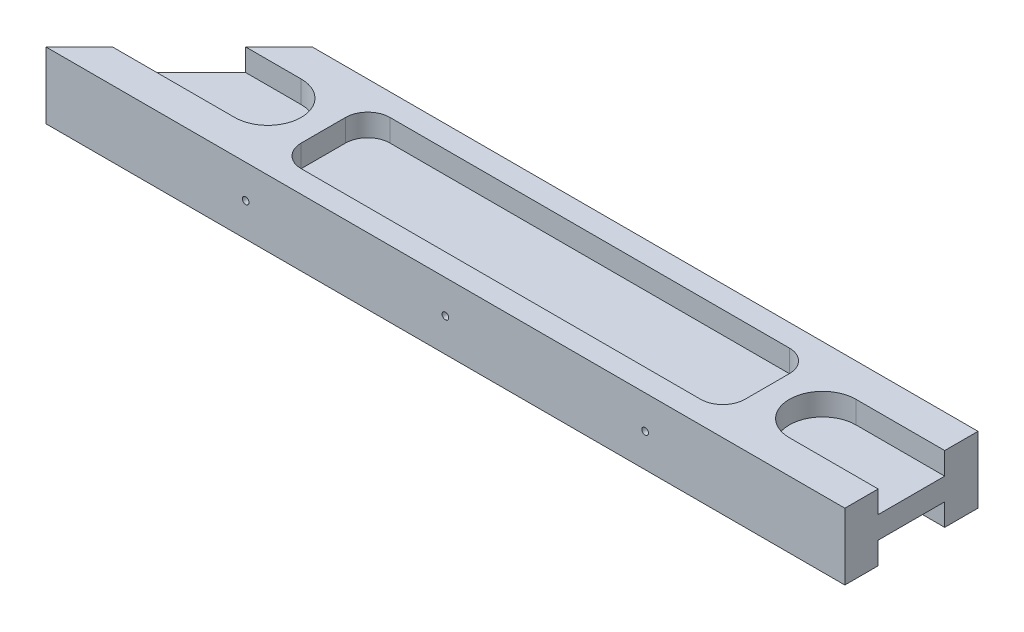
SolidWorks part; units mm, degrees
ref_plane "Front Plane" through (0, 0, 0) normal (0, 0, 1) x (1, 0, 0)
ref_plane "Top Plane" through (0, 0, 0) normal (0, 1, 0) x (1, 0, 0)
ref_plane "Right Plane" through (0, 0, 0) normal (1, 0, 0) x (0, 0, -1)
sketch "Sketch1" plane through (0, 0, 0) normal (0, 1, 0) x (1, 0, 0)
  line L0 (0, 0) -> (180, 0)
  line L1 (180, 0) -> (180, 30)
  line L2 (180, 30) -> (30, 30)
  line L3 (30, 30) -> (0, 0)
  dimension "D1" = 150
  dimension "D2" = 180
  dimension "D3" = 30
extrude "Boss-Extrude1" add sketch "Sketch1" along normal blind 15
sketch "Sketch2" plane through (0, 15, 0) normal (0, 1, 0) x (1, 0, 0)
  line L0 (-5, 15) -> (35, 15) construction
  line L1 (-5, 22.5) -> (35, 22.5)
  line L2 (-5, 7.5) -> (35, 7.5)
  line L3 (30, 30) -> (0, 0) construction
  line L4 (15, 15) -> (180, 15) construction
  line L7 (180, 0) -> (180, 30) construction
  line L8 (97.5, 15) -> (97.5, 30) construction
  line L9 (180, 30) -> (30, 30) construction
  line L10 (200, 15) -> (160, 15) construction
  line L11 (200, 22.5) -> (160, 22.5)
  line L12 (200, 7.5) -> (160, 7.5)
  arc A0 (-5, 22.5) -> (-5, 7.5) centre (-5, 15) ccw
  arc A1 (35, 7.5) -> (35, 22.5) centre (35, 15) ccw
  arc A2 (200, 22.5) -> (200, 7.5) centre (200, 15) cw
  arc A3 (160, 7.5) -> (160, 22.5) centre (160, 15) cw
  point P2 (15, 15)
  point P9 (15, 15)
  point P20 (180, 15)
  dimension "D1" = 40
  dimension "D2" = 15
extrude "Cut-Extrude1" cut sketch "Sketch2" against normal blind 5
sketch "Sketch3" plane through (0, 0, 0) normal (0, -1, 0) x (1, 0, 0)
  line L0 (30, -30) -> (0, 0) construction
  line L1 (180, 0) -> (180, -30) construction
  line L2 (160, -7.5) -> (180, -7.5) construction
  line L3 (180, -22.5) -> (160, -22.5) construction
  line L4 (35, -22.5) -> (22.5, -22.5) construction
  line L5 (7.5, -7.5) -> (35, -7.5) construction
  line L6 (22.5, -22.5) -> (7.5, -7.5)
  line L7 (180, -7.5) -> (180, -22.5)
  line L8 (160, -7.5) -> (180, -7.5)
  line L9 (180, -22.5) -> (160, -22.5)
  line L10 (35, -22.5) -> (22.5, -22.5)
  line L11 (7.5, -7.5) -> (35, -7.5)
  arc A0 (160, -7.5) -> (160, -22.5) centre (160, -15) ccw construction
  arc A1 (35, -22.5) -> (35, -7.5) centre (35, -15) ccw construction
  arc A2 (160, -7.5) -> (160, -22.5) centre (160, -15) ccw
  arc A3 (35, -22.5) -> (35, -7.5) centre (35, -15) ccw
extrude "Cut-Extrude2" cut sketch "Sketch3" against normal blind 5
sketch "Sketch4" plane through (0, 0, 0) normal (0, 0, 1) x (1, 0, 0)
  line L0 (0, 7.5) -> (180, 7.5) construction
  line L1 (0, 15) -> (0, 0) construction
  line L2 (180, 15) -> (180, 0) construction
  circle A0 centre (90, 7.5) radius 0.75
  circle A1 centre (45, 7.5) radius 0.75
  circle A2 centre (135, 7.5) radius 0.75
  dimension "D1" = 1.5
  dimension "D2" = 45
  dimension "D3" = 45
extrude "Cut-Extrude3" cut sketch "Sketch4" against normal up to surface (30 mm away) up to face at (105, 7.5, -30)
sketch "Sketch5" plane through (0, 15, 0) normal (0, 1, 0) x (1, 0, 0)
  line L0 (0, 0) -> (180, 0) construction
  line L1 (52.5, 25) -> (142.5, 25)
  line L2 (47.5, 20) -> (47.5, 10)
  line L3 (52.5, 5) -> (142.5, 5)
  line L4 (147.5, 20) -> (147.5, 10)
  line L5 (180, 30) -> (30, 30) construction
  arc A0 (35, 7.5) -> (35, 22.5) centre (35, 15) ccw construction
  arc A1 (160, 22.5) -> (160, 7.5) centre (160, 15) ccw construction
  arc A2 (142.5, 25) -> (147.5, 20) centre (142.5, 20) cw
  arc A3 (142.5, 5) -> (147.5, 10) centre (142.5, 10) ccw
  arc A4 (47.5, 10) -> (52.5, 5) centre (52.5, 10) ccw
  arc A5 (52.5, 25) -> (47.5, 20) centre (52.5, 20) ccw
  point P4 (42.5, 15)
  point P5 (152.5, 15)
  dimension "D5" = 5
  dimension "D1" = 5
  dimension "D2" = 5
  dimension "D3" = 5
  dimension "D4" = 5
extrude "Cut-Extrude4" cut sketch "Sketch5" against normal blind 5
